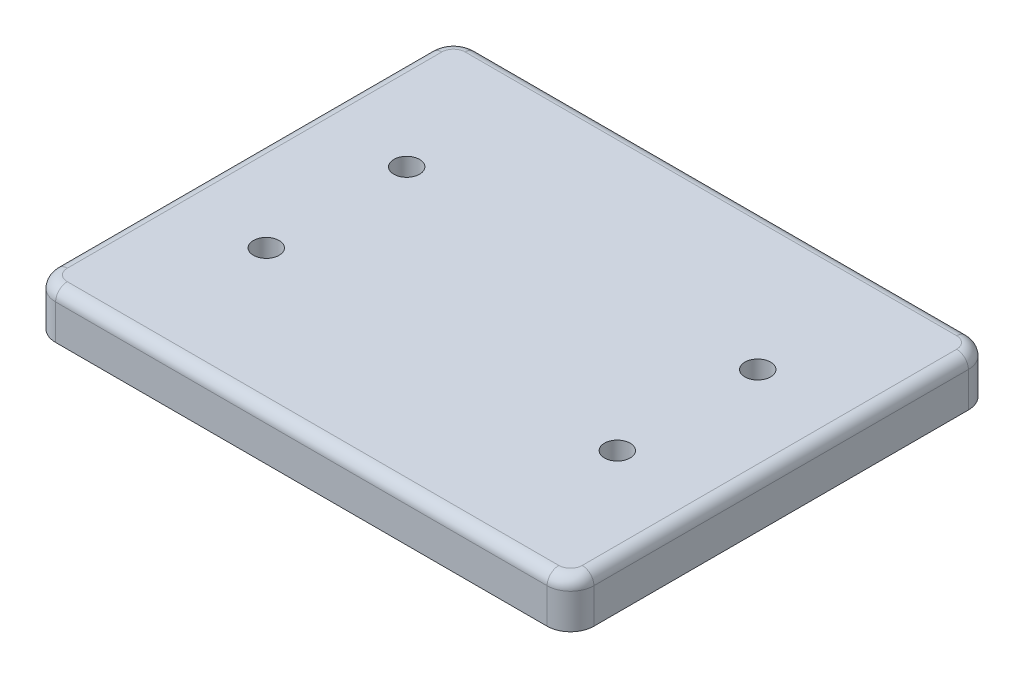
SolidWorks part; units mm, degrees
material "Oak"
ref_plane "Front Plane" through (0, 0, 0) normal (0, 0, 1) x (1, 0, 0)
ref_plane "Top Plane" through (0, 0, 0) normal (0, 1, 0) x (1, 0, 0)
ref_plane "Right Plane" through (0, 0, 0) normal (1, 0, 0) x (0, 0, -1)
sketch "Sketch1" plane through (0, 0, 0) normal (0, 1, 0) x (1, 0, 0)
  line L0 (-521.5686, 0) -> (494.1176, 0) construction
  line L1 (-210, -180) -> (210, -180)
  line L2 (-230, -160) -> (-230, 160)
  line L3 (-210, 180) -> (210, 180)
  line L4 (230, -160) -> (230, 160)
  line L5 (-230, -180) -> (230, 180) construction
  line L6 (-230, 180) -> (230, -180) construction
  line L7 (0, 298.4314) -> (0, -289.8039) construction
  arc A0 (-210, -180) -> (-230, -160) centre (-210, -160) cw
  arc A1 (210, -180) -> (230, -160) centre (210, -160) ccw
  arc A2 (210, 180) -> (230, 160) centre (210, 160) cw
  arc A3 (-230, 160) -> (-210, 180) centre (-210, 160) cw
  circle A4 centre (-150, 60) radius 11
  circle A5 centre (-150, -60) radius 11
  circle A6 centre (150, -60) radius 11
  circle A7 centre (150, 60) radius 11
  point P0 (0, 0)
  dimension "D3" = 20
  dimension "D4" = 60
  dimension "D6" = 22
  dimension "D1" = 360
  dimension "D2" = 460
  dimension "D5" = 150
extrude "Boss-Extrude1" add sketch "Sketch1" along normal blind 40
fillet "Fillet1" radius 10 8 edges at (-224.1421, 40, 174.1421) (-230, 40, 0) (-224.1421, 40, -174.1421) (0, 40, -180) (224.1421, 40, -174.1421) (230, 40, 0) (224.1421, 40, 174.1421) (0, 40, 180)
sketch "Sketch2" plane through (0, 0, 0) normal (0, -1, 0) x (1, 0, 0)
  circle A0 centre (-150, 60) radius 18
  dimension "D1" = 36
extrude "Cut-Extrude1" cut sketch "Sketch2" against normal blind 20
pattern_linear "LPattern1" count 2 spacing 300 along (1, 0, 0) count 2 spacing 120 along (0, 0, -1) of "Cut-Extrude1"
